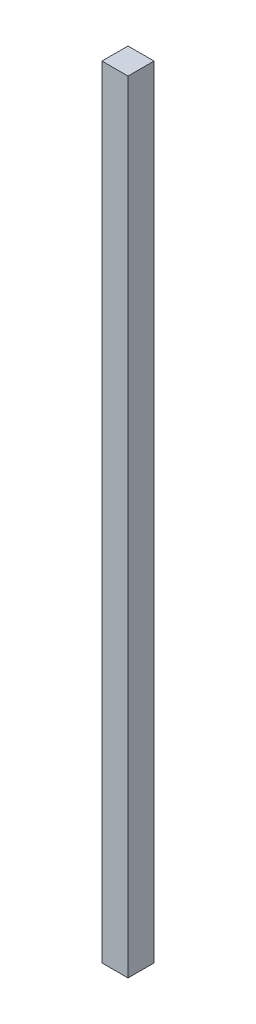
SolidWorks part; units mm, degrees
ref_plane "Front Plane" through (0, 0, 0) normal (0, 0, 1) x (1, 0, 0)
ref_plane "Top Plane" through (0, 0, 0) normal (0, 1, 0) x (1, 0, 0)
ref_plane "Right Plane" through (0, 0, 0) normal (1, 0, 0) x (0, 0, -1)
sketch "Sketch1" plane through (0, 0, 0) normal (0, 1, 0) x (1, 0, 0)
  line L1 (50.8, 50.8) -> (-50.8, 50.8)
  line L2 (50.8, 50.8) -> (50.8, -50.8)
  line L3 (50.8, -50.8) -> (-50.8, -50.8)
  line L4 (-50.8, 50.8) -> (-50.8, -50.8)
  line L5 (50.8, 50.8) -> (-50.8, -50.8) construction
  line L6 (50.8, -50.8) -> (-50.8, 50.8) construction
  point P0 (0, 0)
  dimension "D1" = 101.6
extrude "Boss-Extrude1" add sketch "Sketch1" along normal blind 3048
